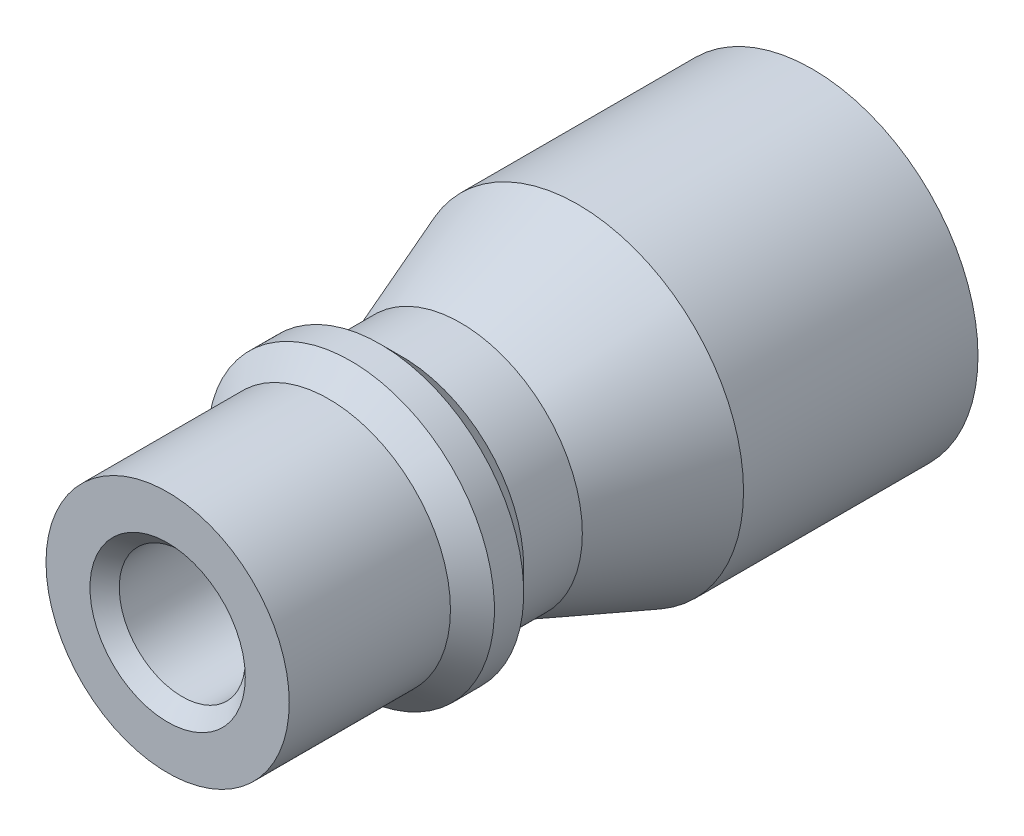
SolidWorks part; units mm, degrees
ref_plane "Front" through (0, 0, 0) normal (0, 0, 1) x (1, 0, 0)
ref_plane "Top" through (0, 0, 0) normal (0, 1, 0) x (1, 0, 0)
ref_plane "Right" through (0, 0, 0) normal (1, 0, 0) x (0, 0, -1)
sketch "Sketch1" plane through (0, 0, 0) normal (0, 0, 1) x (1, 0, 0)
  circle A0 centre (0, 0) radius 3.65
  circle A1 centre (0, 0) radius 5.65
  dimension "D1" = 7.3
  dimension "D2" = 2
extrude "Boss-Extrude1" add sketch "Sketch1" along normal blind 8
ref_plane "Plane1" through (0, 0, 12) normal (0, 0, 1) x (1, 0, 0)
sketch "Sketch3" plane through (0, 0, 8) normal (0, 0, 1) x (1, 0, 0)
  circle A1 centre (0, 0) radius 5.65 construction
  circle A3 centre (0, 0) radius 5.65
sketch "Sketch2" plane through (0, 0, 12) normal (0, 0, 1) x (1, 0, 0)
  circle A1 centre (0, 0) radius 4.15
  dimension "D1" = 8.3
loft "Loft1" add profiles "Sketch3", "Sketch2"
sketch "Sketch4" plane through (0, 0, 8) normal (0, 0, -1) x (-1, 0, 0)
  circle A0 centre (0, 0) radius 3.65 construction
  circle A1 centre (0, 0) radius 3.65
extrude "Cut-Extrude2" cut sketch "Sketch4" against normal blind 3 draft 49
sketch "Sketch6" plane through (0, 0, 12) normal (0, 0, 1) x (1, 0, 0)
  circle A0 centre (0, 0) radius 4.15 construction
  circle A2 centre (0, 0) radius 4.15
  circle A3 centre (0, 0) radius 2.15
  dimension "D1" = 4.3
extrude "Boss-Extrude2" add sketch "Sketch6" along normal blind 10
sketch "Sketch7" plane through (0, 0, 0) normal (1, 0, 0) x (0, 0, -1)
  line L0 (-14, 4.15) -> (-14.75, 4.9)
  line L1 (-12, 4.15) -> (-22, 4.15) construction
  line L2 (-14.75, 4.9) -> (-15.75, 4.9)
  line L3 (-15.75, 4.9) -> (-16.5, 4.15)
  line L4 (-16.5, 4.15) -> (-14, 4.15)
  line L5 (-12, -4.15) -> (-12, 4.15) construction
  dimension "D1" = 0.75
  dimension "D2" = 1
  dimension "D3" = 2
ref_axis "Axis1" through (0, 0, -80.9) along (0, 0, 1)
revolve "Revolve1" add sketch "Sketch7" angle 360 about axis through (0, 0, -80.9) along (0, 0, 1)
chamfer "Chamfer1" distance 0.5 angle 45 1 edges at (3.65, 0, 0)
chamfer "Chamfer2" distance 0.5 angle 45 1 edges at (2.15, 0, 22)
equation "\"RodDiameter\"=4"
equation "\"Delta\"=0.3"
equation "\"D1@Sketch2\" = \"RodDiameter\" + \"Delta\" + 2 * \"WallThickness\""
equation "\"WallThickness\"=2"
equation "\"D1@Sketch6\" = \"RodDiameter\"+\"Delta\""
